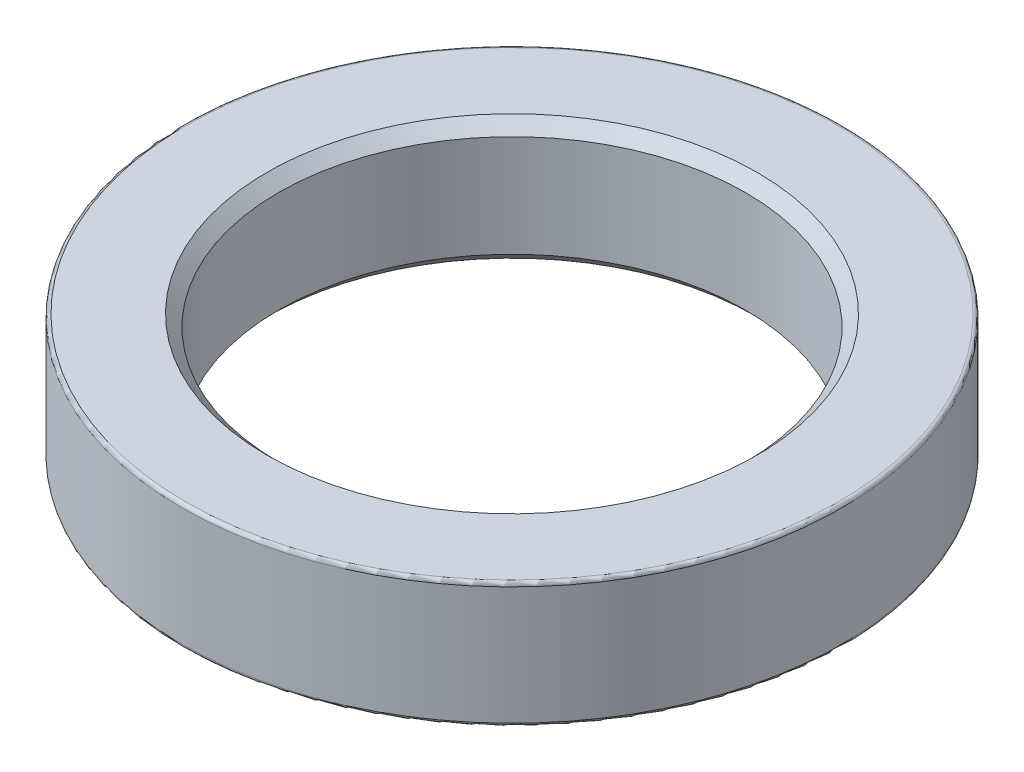
SolidWorks part; units mm, degrees
ref_plane "Front Plane" through (0, 0, 0) normal (0, 0, 1) x (1, 0, 0)
ref_plane "Top Plane" through (0, 0, 0) normal (0, 1, 0) x (1, 0, 0)
ref_plane "Right Plane" through (0, 0, 0) normal (1, 0, 0) x (0, 0, -1)
sketch "Sketch1" plane through (0, 0, 0) normal (0, 1, 0) x (1, 0, 0)
  circle A0 centre (0, 0) radius 35.5981
  dimension "D1" = 71.1962
extrude "Boss-Extrude1" add sketch "Sketch1" along normal blind 13.5128 contours A0
sketch "Sketch2" plane through (0, 13.5128, 0) normal (0, 1, 0) x (1, 0, 0)
  circle A0 centre (0, 0) radius 25.2095
  dimension "D1" = 50.419
extrude "Cut-Extrude1" cut sketch "Sketch2" against normal blind 40.64
fillet "Fillet1" radius 0.381 1 edges at (0, 13.5128, 35.5981)
fillet "Fillet2" radius 0.381 1 edges at (0, 0, 35.5981)
chamfer "Chamfer1" distance 1.2573 angle 45 1 edges at (0, 13.5128, 25.2095)
chamfer "Chamfer2" distance 1.2573 angle 45 1 edges at (0, 0, 25.2095)
